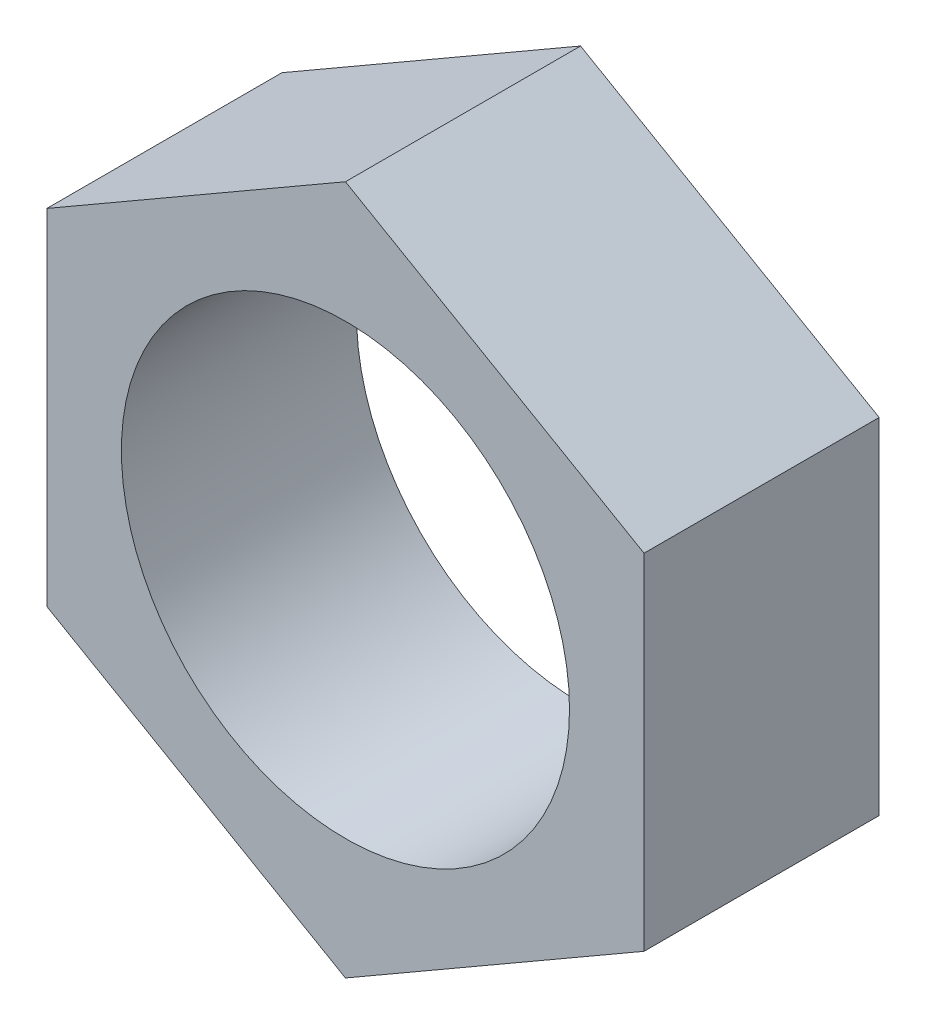
SolidWorks part; units mm, degrees
ref_plane "Alzado" through (0, 0, 0) normal (0, 0, 1) x (1, 0, 0)
ref_plane "Planta" through (0, 0, 0) normal (0, 1, 0) x (1, 0, 0)
ref_plane "Vista lateral" through (0, 0, 0) normal (1, 0, 0) x (0, 0, -1)
sketch "Croquis1" plane through (0, 0, 0) normal (0, 0, 1) x (1, 0, 0)
  line L1 (-6.35, -3.6662) -> (0, -7.3323)
  line L2 (0, -7.3323) -> (6.35, -3.6662)
  line L3 (6.35, -3.6662) -> (6.35, 3.6662)
  line L4 (6.35, 3.6662) -> (0, 7.3323)
  line L5 (0, 7.3323) -> (-6.35, 3.6662)
  line L6 (-6.35, 3.6662) -> (-6.35, -3.6662)
  circle A0 centre (0, 0) radius 6.35 construction
  circle A1 centre (0, 0) radius 4.765
  point P10 (0, 0)
  dimension "D1" = 9.53
  dimension "D2" = 12.7
extrude "Saliente-Extruir1" add sketch "Croquis1" along normal blind 5
